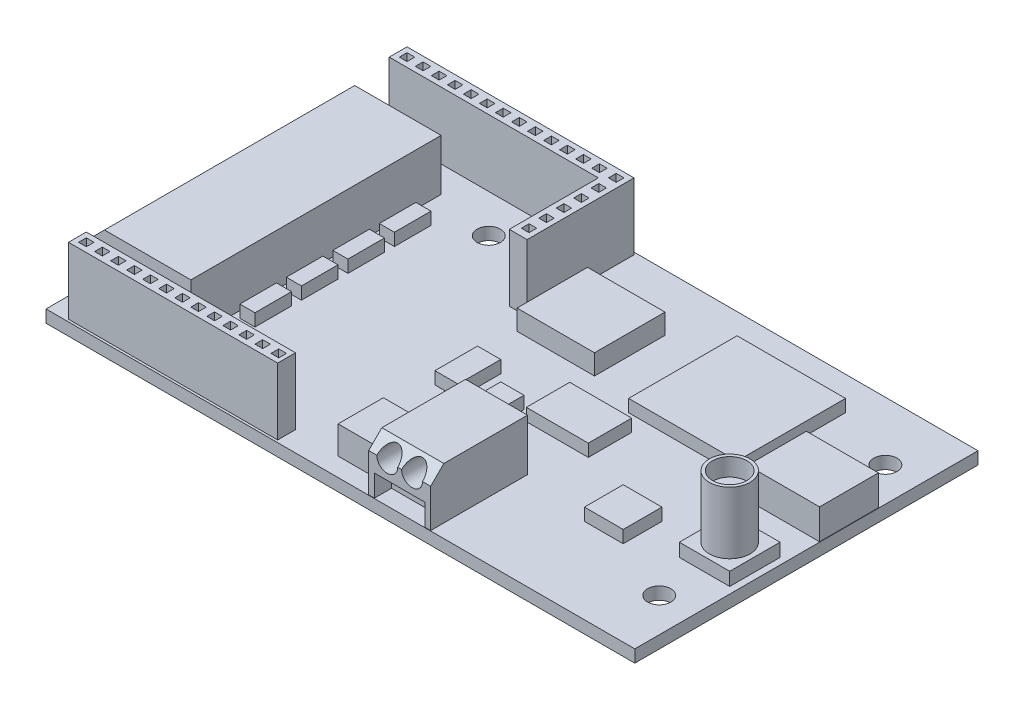
SolidWorks part; units mm, degrees
ref_plane "Front Plane" through (0, 0, 0) normal (0, 0, 1) x (1, 0, 0)
ref_plane "Top Plane" through (0, 0, 0) normal (0, 1, 0) x (1, 0, 0)
ref_plane "Right Plane" through (0, 0, 0) normal (1, 0, 0) x (0, 0, -1)
sketch "Sketch1" plane through (0, 0, 0) normal (0, 1, 0) x (1, 0, 0)
  line L1 (0, 0) -> (76, 0)
  line L2 (0, 0) -> (0, 44.3)
  line L3 (0, 44.3) -> (76, 44.3)
  line L4 (76, 0) -> (76, 44.3)
  circle A0 centre (20.4, 36.75) radius 1.5
  circle A1 centre (71.6, 36.75) radius 1.5
  circle A2 centre (20.4, 7.55) radius 1.5
  circle A3 centre (71.6, 7.55) radius 1.5
  dimension "D1" = 44.3
  dimension "D2" = 76
  dimension "D3" = 51.2
  dimension "D4" = 29.2
extrude "Boss-Extrude1" add sketch "Sketch1" along normal blind 1.6
sketch "Sketch2" plane through (0, 1.6, 0) normal (0, 1, 0) x (1, 0, 0)
  line L1 (0.05, 6) -> (12.7, 6)
  line L3 (0.05, 38.3) -> (12.7, 38.3)
  line L4 (12.7, 6) -> (12.7, 38.3)
  line L5 (0, 44.3) -> (0, 0) construction
  line L6 (0.05, 38.3) -> (0.05, 6)
  point P8 (0, 22.15)
  point P9 (12.7, 22.15)
  dimension "D1" = 32.3
  dimension "D2" = 0
extrude "Boss-Extrude2" add sketch "Sketch2" along normal blind 6.6
chamfer "Chamfer1" distance 1.5 angle 45 1 edges at (0.05, 8.2, -22.15)
sketch "Sketch3" plane through (0.05, 0, 0) normal (-1, 0, 0) x (0, 0, 1)
  line L0 (-38.3, 1.6) -> (-6, 1.6) construction
  line L1 (-37.7, 4.3) -> (-31.2, 4.3)
  line L2 (-37.7, 4.3) -> (-37.7, 1.6)
  line L3 (-37.7, 1.6) -> (-31.2, 1.6)
  line L4 (-31.2, 4.3) -> (-31.2, 1.6)
  line L5 (-38.3, 6.7) -> (-38.3, 1.6) construction
  line L6 (-29.5, 4.3) -> (-23, 4.3)
  line L7 (-23, 4.3) -> (-23, 1.6)
  line L8 (-29.5, 1.6) -> (-23, 1.6)
  line L9 (-29.5, 4.3) -> (-29.5, 1.6)
  line L10 (-21.3, 4.3) -> (-14.8, 4.3)
  line L11 (-14.8, 4.3) -> (-14.8, 1.6)
  line L12 (-21.3, 1.6) -> (-14.8, 1.6)
  line L13 (-21.3, 4.3) -> (-21.3, 1.6)
  line L14 (-13.1, 4.3) -> (-6.6, 4.3)
  line L15 (-6.6, 4.3) -> (-6.6, 1.6)
  line L16 (-13.1, 1.6) -> (-6.6, 1.6)
  line L17 (-13.1, 4.3) -> (-13.1, 1.6)
  dimension "D1" = 6.5
  dimension "D2" = 2.7
  dimension "D3" = 0
  dimension "D4" = 0.6
  dimension "D5" = 4
extrude "Cut-Extrude1" cut sketch "Sketch3" against normal blind 2.5
sketch "Sketch4" plane through (0.05, 0, 0) normal (-1, 0, 0) x (0, 0, 1)
  line L0 (-6, 6.7) -> (-38.3, 6.7) construction
  line L1 (-31.2, 4.3) -> (-37.7, 4.3) construction
  circle A0 centre (-36.05, 6.7) radius 1.35
  circle A1 centre (-32.85, 6.7) radius 1.35
  point P8 (-34.45, 4.3)
  dimension "D1" = 2.7
  dimension "D2" = 2.7
  dimension "D3" = 3.2
  dimension "D4" = 1.6
extrude "Cut-Extrude2" cut sketch "Sketch4" against normal blind 12
pattern_linear "LPattern1" count 4 spacing 8.2 along (0, 0, 1) of "Cut-Extrude2"
sketch "Sketch5" plane through (0, 1.6, 0) normal (0, 1, 0) x (1, 0, 0)
  line L0 (76, 44.3) -> (0, 44.3) construction
  line L1 (2.6, 44) -> (31.9, 44)
  line L2 (2.6, 44) -> (2.6, 41.7)
  line L3 (2.6, 41.7) -> (29.6, 41.7)
  line L4 (31.9, 44) -> (31.9, 41.7)
  line L5 (31.9, 44) -> (28.1061, 44)
  line L6 (31.9, 44) -> (31.9, 30.2)
  line L7 (31.9, 30.2) -> (29.6, 30.2)
  line L8 (29.6, 41.7) -> (29.6, 30.2)
  line L9 (2.6, 0.3) -> (29.6, 0.3)
  line L10 (2.6, 0.3) -> (2.6, 2.6)
  line L11 (2.6, 2.6) -> (29.6, 2.6)
  line L12 (29.6, 0.3) -> (29.6, 2.6)
  line L13 (0, 0) -> (76, 0) construction
  line L14 (0, 44.3) -> (0, 0) construction
  line L15 (6.32, 42.35) -> (6.32, 43.35)
  line L16 (4.25, 42.35) -> (3.25, 42.35)
  line L17 (4.25, 42.35) -> (4.25, 43.35)
  line L18 (4.25, 43.35) -> (3.25, 43.35)
  line L19 (3.25, 42.35) -> (3.25, 43.35)
  line L20 (6.32, 42.35) -> (5.32, 42.35)
  line L21 (5.32, 42.35) -> (5.32, 43.35)
  line L22 (6.32, 43.35) -> (5.32, 43.35)
  line L23 (8.39, 42.35) -> (8.39, 43.35)
  line L24 (8.39, 42.35) -> (7.39, 42.35)
  line L25 (7.39, 42.35) -> (7.39, 43.35)
  line L26 (8.39, 43.35) -> (7.39, 43.35)
  line L27 (10.46, 42.35) -> (10.46, 43.35)
  line L28 (10.46, 42.35) -> (9.46, 42.35)
  line L29 (9.46, 42.35) -> (9.46, 43.35)
  line L30 (10.46, 43.35) -> (9.46, 43.35)
  line L31 (12.53, 42.35) -> (12.53, 43.35)
  line L32 (12.53, 42.35) -> (11.53, 42.35)
  line L33 (11.53, 42.35) -> (11.53, 43.35)
  line L34 (12.53, 43.35) -> (11.53, 43.35)
  line L35 (14.6, 42.35) -> (14.6, 43.35)
  line L36 (14.6, 42.35) -> (13.6, 42.35)
  line L37 (13.6, 42.35) -> (13.6, 43.35)
  line L38 (14.6, 43.35) -> (13.6, 43.35)
  line L39 (16.67, 42.35) -> (16.67, 43.35)
  line L40 (16.67, 42.35) -> (15.67, 42.35)
  line L41 (15.67, 42.35) -> (15.67, 43.35)
  line L42 (16.67, 43.35) -> (15.67, 43.35)
  line L43 (18.74, 42.35) -> (18.74, 43.35)
  line L44 (18.74, 42.35) -> (17.74, 42.35)
  line L45 (17.74, 42.35) -> (17.74, 43.35)
  line L46 (18.74, 43.35) -> (17.74, 43.35)
  line L47 (20.81, 42.35) -> (20.81, 43.35)
  line L48 (20.81, 42.35) -> (19.81, 42.35)
  line L49 (19.81, 42.35) -> (19.81, 43.35)
  line L50 (20.81, 43.35) -> (19.81, 43.35)
  line L51 (22.88, 42.35) -> (22.88, 43.35)
  line L52 (22.88, 42.35) -> (21.88, 42.35)
  line L53 (21.88, 42.35) -> (21.88, 43.35)
  line L54 (22.88, 43.35) -> (21.88, 43.35)
  line L55 (24.95, 42.35) -> (24.95, 43.35)
  line L56 (24.95, 42.35) -> (23.95, 42.35)
  line L57 (23.95, 42.35) -> (23.95, 43.35)
  line L58 (24.95, 43.35) -> (23.95, 43.35)
  line L59 (27.02, 42.35) -> (27.02, 43.35)
  line L60 (27.02, 42.35) -> (26.02, 42.35)
  line L61 (26.02, 42.35) -> (26.02, 43.35)
  line L62 (27.02, 43.35) -> (26.02, 43.35)
  line L63 (29.09, 42.35) -> (29.09, 43.35)
  line L64 (29.09, 42.35) -> (28.09, 42.35)
  line L65 (28.09, 42.35) -> (28.09, 43.35)
  line L66 (29.09, 43.35) -> (28.09, 43.35)
  line L67 (6.32, 0.95) -> (6.32, 1.95)
  line L68 (6.32, 0.95) -> (5.32, 0.95)
  line L69 (5.32, 0.95) -> (5.32, 1.95)
  line L70 (6.32, 1.95) -> (5.32, 1.95)
  line L71 (8.39, 0.95) -> (8.39, 1.95)
  line L72 (8.39, 0.95) -> (7.39, 0.95)
  line L73 (7.39, 0.95) -> (7.39, 1.95)
  line L74 (8.39, 1.95) -> (7.39, 1.95)
  line L75 (10.46, 0.95) -> (10.46, 1.95)
  line L76 (10.46, 0.95) -> (9.46, 0.95)
  line L77 (9.46, 0.95) -> (9.46, 1.95)
  line L78 (10.46, 1.95) -> (9.46, 1.95)
  line L79 (12.53, 0.95) -> (12.53, 1.95)
  line L80 (12.53, 0.95) -> (11.53, 0.95)
  line L81 (11.53, 0.95) -> (11.53, 1.95)
  line L82 (12.53, 1.95) -> (11.53, 1.95)
  line L83 (14.6, 0.95) -> (14.6, 1.95)
  line L84 (14.6, 0.95) -> (13.6, 0.95)
  line L85 (13.6, 0.95) -> (13.6, 1.95)
  line L86 (14.6, 1.95) -> (13.6, 1.95)
  line L87 (16.67, 0.95) -> (16.67, 1.95)
  line L88 (16.67, 0.95) -> (15.67, 0.95)
  line L89 (15.67, 0.95) -> (15.67, 1.95)
  line L90 (16.67, 1.95) -> (15.67, 1.95)
  line L91 (18.74, 0.95) -> (18.74, 1.95)
  line L92 (18.74, 0.95) -> (17.74, 0.95)
  line L93 (17.74, 0.95) -> (17.74, 1.95)
  line L94 (18.74, 1.95) -> (17.74, 1.95)
  line L95 (20.81, 0.95) -> (20.81, 1.95)
  line L96 (20.81, 0.95) -> (19.81, 0.95)
  line L97 (19.81, 0.95) -> (19.81, 1.95)
  line L98 (20.81, 1.95) -> (19.81, 1.95)
  line L99 (22.88, 0.95) -> (22.88, 1.95)
  line L100 (22.88, 0.95) -> (21.88, 0.95)
  line L101 (21.88, 0.95) -> (21.88, 1.95)
  line L102 (22.88, 1.95) -> (21.88, 1.95)
  line L103 (24.95, 0.95) -> (24.95, 1.95)
  line L104 (24.95, 0.95) -> (23.95, 0.95)
  line L105 (23.95, 0.95) -> (23.95, 1.95)
  line L106 (24.95, 1.95) -> (23.95, 1.95)
  line L107 (27.02, 0.95) -> (27.02, 1.95)
  line L108 (27.02, 0.95) -> (26.02, 0.95)
  line L109 (26.02, 0.95) -> (26.02, 1.95)
  line L110 (27.02, 1.95) -> (26.02, 1.95)
  line L111 (29.09, 0.95) -> (29.09, 1.95)
  line L112 (29.09, 0.95) -> (28.09, 0.95)
  line L113 (28.09, 0.95) -> (28.09, 1.95)
  line L114 (29.09, 1.95) -> (28.09, 1.95)
  line L115 (4.25, 0.95) -> (4.25, 1.95)
  line L116 (4.25, 0.95) -> (3.25, 0.95)
  line L117 (3.25, 0.95) -> (3.25, 1.95)
  line L118 (4.25, 1.95) -> (3.25, 1.95)
  line L119 (31.25, 41.1) -> (31.25, 40.1)
  line L120 (30.25, 43.35) -> (31.25, 43.35)
  line L121 (30.25, 43.35) -> (30.25, 42.35)
  line L122 (30.25, 42.35) -> (31.25, 42.35)
  line L123 (31.25, 43.35) -> (31.25, 42.35)
  line L124 (30.25, 40.1) -> (31.25, 40.1)
  line L125 (30.25, 41.1) -> (30.25, 40.1)
  line L126 (30.25, 41.1) -> (31.25, 41.1)
  line L127 (31.25, 38.85) -> (31.25, 37.85)
  line L128 (30.25, 37.85) -> (31.25, 37.85)
  line L129 (30.25, 38.85) -> (30.25, 37.85)
  line L130 (30.25, 38.85) -> (31.25, 38.85)
  line L131 (31.25, 36.6) -> (31.25, 35.6)
  line L132 (30.25, 35.6) -> (31.25, 35.6)
  line L133 (30.25, 36.6) -> (30.25, 35.6)
  line L134 (30.25, 36.6) -> (31.25, 36.6)
  line L135 (31.25, 34.35) -> (31.25, 33.35)
  line L136 (30.25, 33.35) -> (31.25, 33.35)
  line L137 (30.25, 34.35) -> (30.25, 33.35)
  line L138 (30.25, 34.35) -> (31.25, 34.35)
  line L139 (31.25, 32.1) -> (31.25, 31.1)
  line L140 (30.25, 31.1) -> (31.25, 31.1)
  line L141 (30.25, 32.1) -> (30.25, 31.1)
  line L142 (30.25, 32.1) -> (31.25, 32.1)
  point P22 (3.25, 42.85)
  point P23 (2.6, 42.85)
  point P128 (30.75, 43.35)
  point P129 (30.75, 30.2)
  dimension "D1" = 2.3
  dimension "D2" = 2.3
  dimension "D3" = 2.3
  dimension "D4" = 27
  dimension "D5" = 27
  dimension "D6" = 13.8
  dimension "D7" = 0.3
  dimension "D8" = 0.3
  dimension "D9" = 2.6
  dimension "D10" = 2.6
  dimension "D11" = 1
  dimension "D12" = 1
  dimension "D13" = 0
  dimension "D14" = 0.65
  dimension "D17" = 1
  dimension "D18" = 0
  dimension "D15" = 13
  dimension "D16" = 2
  dimension "D19" = 6
extrude "Boss-Extrude3" add sketch "Sketch5" along normal blind 8.6 contours L3 L8 L7 L6 L4 L1 L2 L66 L63 L64 L65 L62 L59 L60 L61 L58 L55 L56 L57 L54 L51 L52 L53 L50 L47 L48 L49 L46 L43 L44 L45 L42 L39 L40 L41 L38 L35 L36 L37 L34 L31 | L9 L12 L11 L10 L118 L115 L116 L117 L114 L111 L112 L113 L110 L107 L108 L109 L106 L103 L104 L105 L102 L99 L100 L101 L98 L95 L96 L97 L94 L91 L92 L93 L90 L87 L88 L89 L86 L83 L84 L85 L82
sketch "Sketch6" plane through (0, 1.6, 0) normal (0, 1, 0) x (1, 0, 0)
  line L0 (31.9, 44) -> (31.9, 30.2) construction
  line L1 (32.9, 37) -> (42.9, 37)
  line L2 (32.9, 37) -> (32.9, 27.9)
  line L3 (32.9, 27.9) -> (42.9, 27.9)
  line L4 (42.9, 37) -> (42.9, 27.9)
  line L5 (76, 44.3) -> (0, 44.3) construction
  dimension "D1" = 9.1
  dimension "D2" = 10
  dimension "D3" = 1
  dimension "D4" = 7.3
extrude "Boss-Extrude4" add sketch "Sketch6" along normal blind 2.6
sketch "Sketch7" plane through (0, 1.6, 0) normal (0, 1, 0) x (1, 0, 0)
  line L0 (0, 0) -> (76, 0) construction
  line L1 (41.6, 0.05) -> (49.6, 0.05)
  line L2 (41.6, 0.05) -> (41.6, 12.55)
  line L3 (41.6, 12.55) -> (49.6, 12.55)
  line L4 (49.6, 0.05) -> (49.6, 12.55)
  line L5 (29.6, 0.3) -> (29.6, 2.6) construction
  dimension "D1" = 0.05
  dimension "D2" = 8
  dimension "D3" = 12.5
  dimension "D4" = 12
extrude "Boss-Extrude5" add sketch "Sketch7" along normal blind 6.65
chamfer "Chamfer2" distance 1.7 angle 45 1 edges at (45.6, 8.25, -0.05)
sketch "Sketch8" plane through (0, 0, -0.05) normal (0, 0, 1) x (1, 0, 0)
  line L0 (42.35, 4.4) -> (42.35, 1.6)
  line L1 (42.35, 4.4) -> (48.85, 4.4)
  line L2 (42.35, 1.6) -> (48.85, 1.6)
  line L3 (48.85, 4.4) -> (48.85, 1.6)
  line L4 (42.35, 4.4) -> (48.85, 1.6) construction
  line L5 (42.35, 1.6) -> (48.85, 4.4) construction
  line L6 (49.6, 6.55) -> (41.6, 6.55) construction
  line L7 (0, 1.6) -> (76, 1.6) construction
  point P1 (45.6, 3)
  point P3 (45.6, 6.55)
  dimension "D1" = 6.5
  dimension "D2" = 0
  dimension "D3" = 2.8
  dimension "D4" = 0
extrude "Cut-Extrude3" cut sketch "Sketch8" against normal blind 2.2
sketch "Sketch9" plane through (0, 0, -0.05) normal (0, 0, 1) x (1, 0, 0)
  line L0 (49.6, 6.55) -> (41.6, 6.55) construction
  line L1 (48.85, 4.4) -> (42.35, 4.4) construction
  circle A0 centre (44, 6.55) radius 1.35
  circle A1 centre (47.2, 6.55) radius 1.35
  point P8 (45.6, 4.4)
  dimension "D1" = 2.7
  dimension "D2" = 2.7
  dimension "D3" = 3.2
  dimension "D4" = 1.6
extrude "Cut-Extrude4" cut sketch "Sketch9" against normal blind 12
sketch "Sketch10" plane through (0, 1.6, 0) normal (0, 1, 0) x (1, 0, 0)
  line L0 (13.5634, 28.1809) -> (13.5634, 23.4585)
  line L1 (49.2, 40) -> (63.2, 40)
  line L2 (49.2, 40) -> (49.2, 26)
  line L3 (49.2, 26) -> (63.2, 26)
  line L4 (63.2, 40) -> (63.2, 26)
  line L5 (51.6, 24) -> (43.6, 24)
  line L6 (51.6, 24) -> (51.6, 18.4)
  line L7 (51.6, 18.4) -> (43.6, 18.4)
  line L8 (43.6, 24) -> (43.6, 18.4)
  line L9 (63.5, 16) -> (58.5, 16)
  line L10 (63.5, 16) -> (63.5, 11)
  line L11 (63.5, 11) -> (58.5, 11)
  line L12 (58.5, 16) -> (58.5, 11)
  line L13 (42.1, 19.6) -> (39.1, 19.6)
  line L14 (42.1, 19.6) -> (42.1, 16.6)
  line L15 (42.1, 16.6) -> (39.1, 16.6)
  line L16 (39.1, 19.6) -> (39.1, 16.6)
  line L17 (36.6, 16.6) -> (33.6, 16.6)
  line L18 (36.6, 16.6) -> (36.6, 22.1)
  line L19 (36.6, 22.1) -> (33.6, 22.1)
  line L20 (33.6, 16.6) -> (33.6, 22.1)
  line L21 (13.5634, 34.1809) -> (15.5123, 34.1809)
  line L22 (13.5634, 34.1809) -> (13.5634, 29.4585)
  line L23 (13.5634, 29.4585) -> (15.5123, 29.4585)
  line L24 (15.5123, 34.1809) -> (15.5123, 29.4585)
  line L25 (13.5634, 28.1809) -> (15.5123, 28.1809)
  line L26 (15.5123, 28.1809) -> (15.5123, 23.4585)
  line L27 (13.5634, 23.4585) -> (15.5123, 23.4585)
  line L28 (13.5634, 22.1809) -> (13.5634, 17.4585)
  line L29 (13.5634, 22.1809) -> (15.5123, 22.1809)
  line L30 (15.5123, 22.1809) -> (15.5123, 17.4585)
  line L31 (13.5634, 17.4585) -> (15.5123, 17.4585)
  line L32 (13.5634, 16.1809) -> (13.5634, 11.4585)
  line L33 (13.5634, 16.1809) -> (15.5123, 16.1809)
  line L34 (15.5123, 16.1809) -> (15.5123, 11.4585)
  line L35 (13.5634, 11.4585) -> (15.5123, 11.4585)
  line L36 (76, 44.3) -> (0, 44.3) construction
  line L37 (42.9, 27.9) -> (42.9, 37) construction
  line L38 (76, 0) -> (76, 44.3) construction
  dimension "D2" = 14
  dimension "D3" = 14
  dimension "D4" = 4.3
  dimension "D5" = 6.3
  dimension "D6" = 8
  dimension "D7" = 5.6
  dimension "D8" = 2
  dimension "D9" = 1.5
  dimension "D10" = 2.4
  dimension "D11" = 1.8
  dimension "D12" = 0
  dimension "D13" = 2.5
  dimension "D14" = 3
  dimension "D15" = 3
  dimension "D16" = 5.5
  dimension "D17" = 3
  dimension "D18" = 5
  dimension "D19" = 5
  dimension "D20" = 10
  dimension "D21" = 12.5
  dimension "D1" = 4
extrude "Boss-Extrude6" add sketch "Sketch10" along normal blind 1.6
sketch "Sketch11" plane through (0, 1.6, 0) normal (0, 1, 0) x (1, 0, 0)
  line L0 (76, 0) -> (76, 44.3) construction
  line L1 (75.95, 31.5) -> (66.65, 31.5)
  line L2 (75.95, 31.5) -> (75.95, 23.9)
  line L3 (75.95, 23.9) -> (66.65, 23.9)
  line L4 (66.65, 31.5) -> (66.65, 23.9)
  line L5 (76, 44.3) -> (0, 44.3) construction
  dimension "D1" = 0.05
  dimension "D2" = 9.3
  dimension "D3" = 7.6
  dimension "D4" = 12.8
extrude "Boss-Extrude7" add sketch "Sketch11" along normal blind 3.9
sketch "Sketch12" plane through (0, 1.6, 0) normal (0, 1, 0) x (1, 0, 0)
  line L0 (66.65, 23.9) -> (75.95, 23.9) construction
  line L1 (75.15, 19.6) -> (68.65, 19.6)
  line L2 (75.15, 19.6) -> (75.15, 13.1)
  line L3 (75.15, 13.1) -> (68.65, 13.1)
  line L4 (68.65, 19.6) -> (68.65, 13.1)
  line L5 (76, 0) -> (76, 44.3) construction
  dimension "D1" = 4.3
  dimension "D2" = 6.5
  dimension "D3" = 6.5
  dimension "D4" = 0.85
extrude "Boss-Extrude8" add sketch "Sketch12" along normal blind 1.7
sketch "Sketch13" plane through (0, 3.3, 0) normal (0, 1, 0) x (1, 0, 0)
  circle A0 centre (71.9, 16.35) radius 2.625
extrude "Boss-Extrude9" add sketch "Sketch13" along normal blind 8
sketch "Sketch14" plane through (0, 11.3, 0) normal (0, 1, 0) x (1, 0, 0)
  circle A0 centre (71.9, 16.35) radius 2.225
  circle A1 centre (71.9, 16.35) radius 2.625 construction
  dimension "D1" = 0.4
extrude "Cut-Extrude5" cut sketch "Sketch14" against normal blind 2.3
sketch "Sketch15" plane through (0, 1.6, 0) normal (0, 1, 0) x (1, 0, 0)
  line L0 (41.6, 12.55) -> (41.6, 0.05) construction
  line L1 (35.3, 8.25) -> (41.1, 8.25)
  line L2 (35.3, 8.25) -> (35.3, 2.4)
  line L3 (35.3, 2.4) -> (41.1, 2.4)
  line L4 (41.1, 8.25) -> (41.1, 2.4)
  line L5 (0, 0) -> (76, 0) construction
  dimension "D1" = 5.85
  dimension "D2" = 5.8
  dimension "D3" = 0.5
  dimension "D4" = 2.4
extrude "Boss-Extrude10" add sketch "Sketch15" along normal blind 3.6
